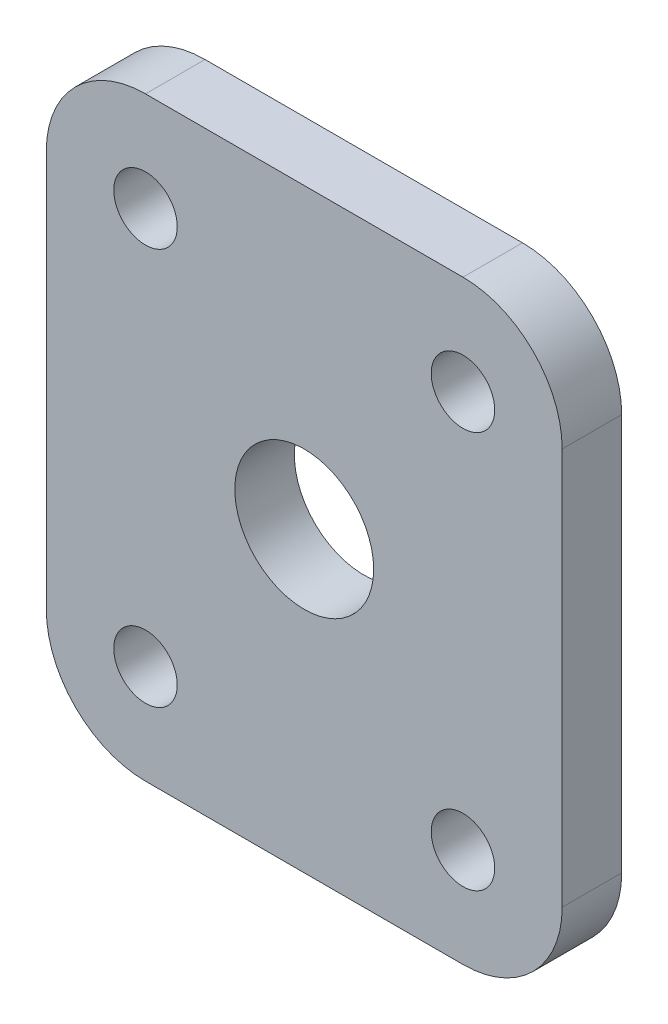
SolidWorks part; units mm, degrees
material "Acrílico (médio-alto impacto)"
ref_plane "Plano frontal" through (0, 0, 0) normal (0, 0, 1) x (1, 0, 0)
ref_plane "Plano superior" through (0, 0, 0) normal (0, 1, 0) x (1, 0, 0)
ref_plane "Plano direito" through (0, 0, 0) normal (1, 0, 0) x (0, 0, -1)
sketch "Esboço1" plane through (0, 0, 0) normal (0, 0, 1) x (1, 0, 0)
  line L1 (-13, -15) -> (13, -15)
  line L2 (-13, -15) -> (-13, 15)
  line L3 (-13, 15) -> (13, 15)
  line L4 (13, -15) -> (13, 15)
  line L5 (0, 15) -> (0, -15) construction
  line L6 (-13, 0) -> (13, 0) construction
  circle A0 centre (-8, 10) radius 1.6
  circle A2 centre (8, 10) radius 1.6
  circle A3 centre (8, -10) radius 1.6
  circle A4 centre (-8, -10) radius 1.6
  circle A5 centre (0, 0) radius 3.5
  point P0 (0, 0)
  dimension "D1" = 16
  dimension "D2" = 20
  dimension "D3" = 5
  dimension "D5" = 3.2
  dimension "D6" = 7
  dimension "D4" = 5
extrude "Ressalto-extrusão1" add sketch "Esboço1" along normal blind 3 contours L1 L4 L3 L2 A5 A2 A0 A3 A4
fillet "Filete1" radius 5 4 edges at (-13, -15, 1.5) (13, -15, 1.5) (-13, 15, 1.5) (13, 15, 1.5)
